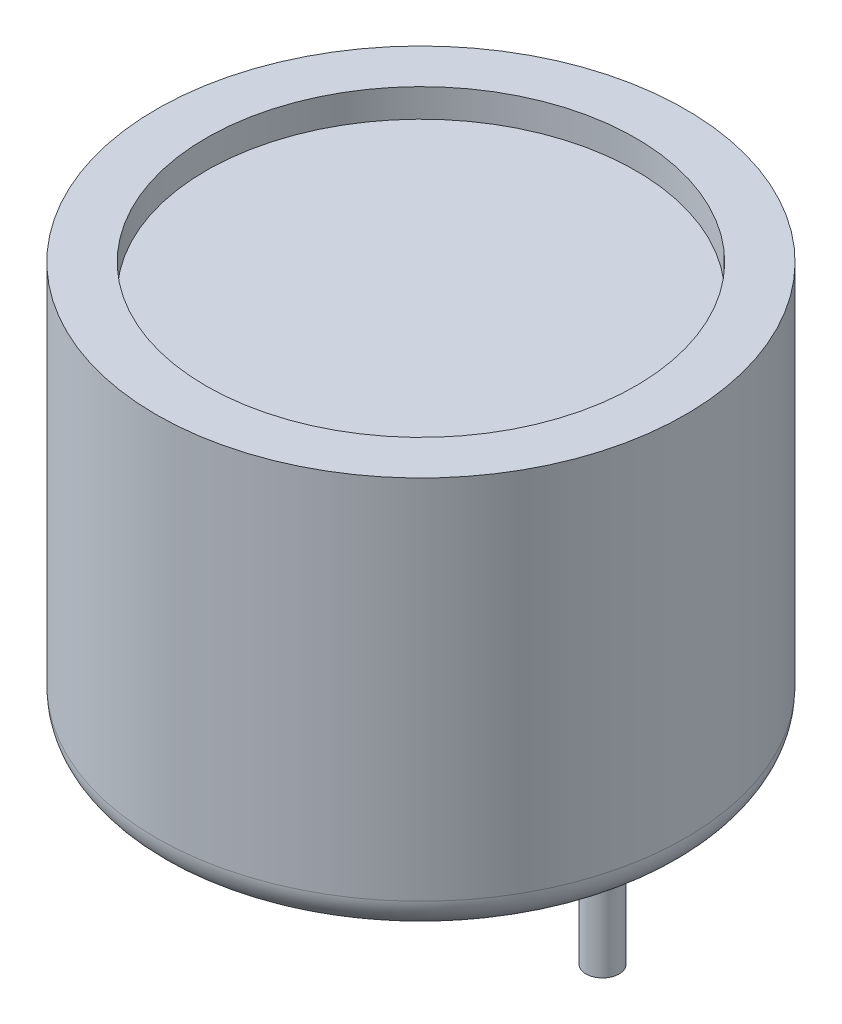
SolidWorks part; units mm, degrees
ref_plane "Front Plane" through (0, 0, 0) normal (0, 0, 1) x (1, 0, 0)
ref_plane "Top Plane" through (0, 0, 0) normal (0, 1, 0) x (1, 0, 0)
ref_plane "Right Plane" through (0, 0, 0) normal (1, 0, 0) x (0, 0, -1)
sketch "Sketch1" plane through (0, 0, 0) normal (0, 1, 0) x (1, 0, 0)
  circle A0 centre (0, 0) radius 7.975
  dimension "D1" = 15.95
extrude "Boss-Extrude1" add sketch "Sketch1" along normal blind 12.05
fillet "Fillet1" radius 1 1 edges at (0, 0, 7.975)
sketch "Sketch3" plane through (0, 0, 0) normal (0, -1, 0) x (1, 0, 0)
  circle A0 centre (0, 0) radius 6.975
  circle A1 centre (0, 0) radius 6.975 construction
extrude "Cut-Extrude1" cut sketch "Sketch3" against normal blind 0.75
sketch "Sketch4" plane through (0, 0.75, 0) normal (0, -1, 0) x (1, 0, 0)
  line L1 (-6.975, 0) -> (-5.475, 0) construction
  line L2 (6.975, 0) -> (5.475, 0) construction
  circle A1 centre (0, 0) radius 6.975 construction
  circle A2 centre (-5.475, 0) radius 0.5
  circle A3 centre (5.475, 0) radius 0.5
  dimension "D3" = 1
  dimension "D4" = 1
  dimension "D1" = 1.5
  dimension "D2" = 1.5
extrude "Boss-Extrude2" add sketch "Sketch4" along normal blind 4.3
sketch "Sketch5" plane through (0, 12.05, 0) normal (0, 1, 0) x (1, 0, 0)
  line L0 (-7.975, 0) -> (-6.475, 0) construction
  circle A3 centre (0, 0) radius 7.975 construction
  circle A4 centre (0, 0) radius 6.475
  dimension "D1" = 1.5
extrude "Cut-Extrude2" cut sketch "Sketch5" against normal blind 0.85
